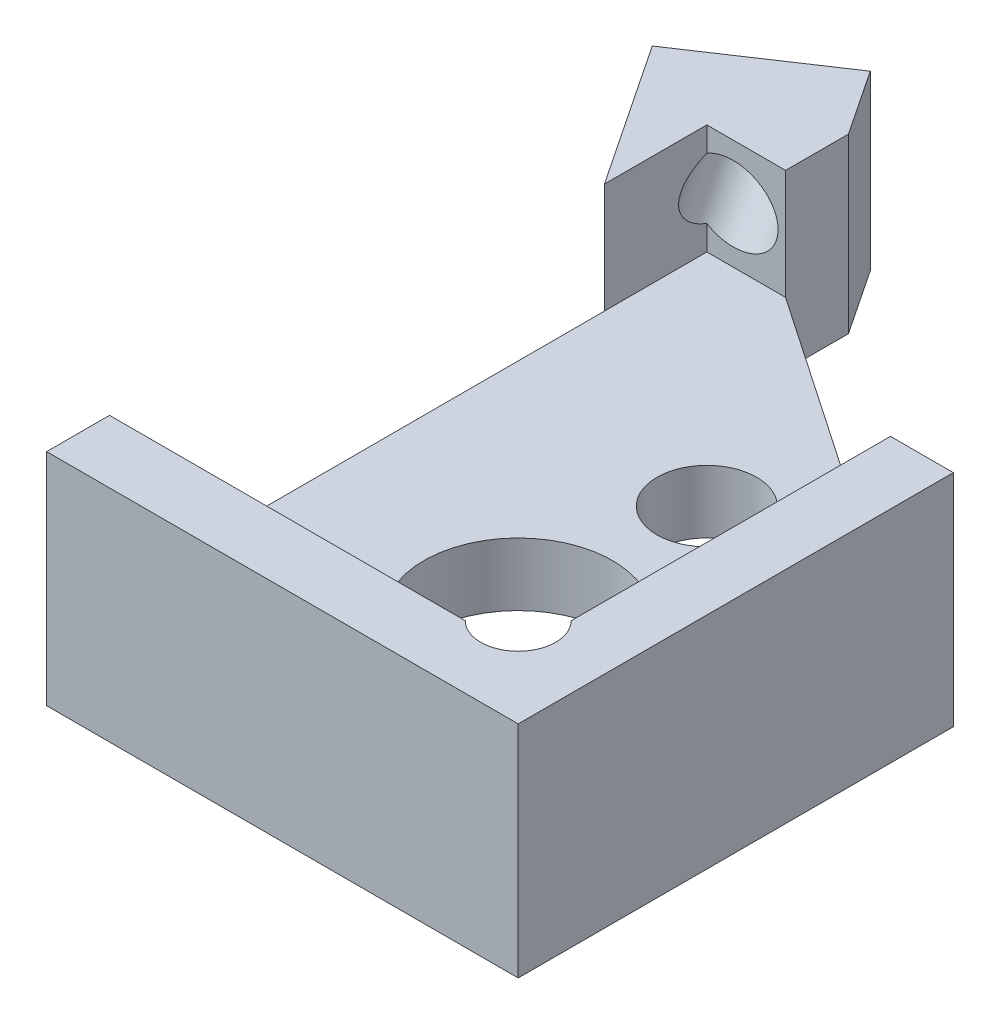
SolidWorks part; units mm, degrees
ref_plane "Front Plane" through (0, 0, 0) normal (0, 0, 1) x (1, 0, 0)
ref_plane "Top Plane" through (0, 0, 0) normal (0, 1, 0) x (1, 0, 0)
ref_plane "Right Plane" through (0, 0, 0) normal (1, 0, 0) x (0, 0, -1)
sketch "Sketch1" plane through (0, 0, 0) normal (0, 1, 0) x (1, 0, 0)
  line L7 (4.25, 5.75) -> (-4.25, 5.75)
  line L8 (4.25, 5.75) -> (4.25, -5.75)
  line L9 (4.25, -5.75) -> (-4.25, -5.75)
  line L10 (-4.25, 5.75) -> (-4.25, -5.75)
  line L11 (4.25, 5.75) -> (-4.25, -5.75) construction
  line L12 (4.25, -5.75) -> (-4.25, 5.75) construction
  point P0 (0, 0)
  point P6 (0, 0)
  dimension "D1" = 8.5
  dimension "D2" = 11.5
extrude "Boss-Extrude1" add sketch "Sketch1" along normal blind 3.5
sketch "Sketch2" plane through (0, 3.5, 0) normal (0, 1, 0) x (1, 0, 0)
  line L0 (-4.25, 5.75) -> (-4.25, -5.75) construction
  line L1 (3.25, 4.75) -> (-3.25, 4.75)
  line L2 (3.25, 4.75) -> (3.25, -4.75)
  line L3 (3.25, -4.75) -> (-3.25, -4.75)
  line L4 (-3.25, 4.75) -> (-3.25, -4.75)
  line L5 (3.25, 4.75) -> (-3.25, -4.75) construction
  line L6 (3.25, -4.75) -> (-3.25, 4.75) construction
  line L7 (4.25, 5.75) -> (-4.25, 5.75) construction
  point P0 (0, 0)
  dimension "D1" = 1
  dimension "D2" = 1
extrude "Cut-Extrude1" cut sketch "Sketch2" against normal offset from surface (2.5 mm away) 1 up to face at (0, 0, 0)
sketch "Sketch3" plane through (0, 1, 0) normal (0, 1, 0) x (1, 0, 0)
  line L0 (-3.25, -4.75) -> (3.25, -4.75) construction
  line L1 (3.25, -4.75) -> (3.25, 4.75) construction
  circle A0 centre (0.25, -1.75) radius 1.5
  dimension "D1" = 3
  dimension "D2" = 3
  dimension "D3" = 3
extrude "Cut-Extrude2" cut sketch "Sketch3" against normal through all
sketch "Sketch6" plane through (0, 3.5, 0) normal (0, 1, 0) x (1, 0, 0)
  line L0 (3.25, -4.75) -> (3.25, 4.75) construction
  line L2 (-3.25, -4.75) -> (3.25, -4.75) construction
  line L3 (3.25, -4.3291) -> (2.8291, -4.3291) construction
  line L4 (2.8291, -4.3291) -> (2.8291, -4.75) construction
  circle A3 centre (2.8291, -4.3291) radius 0.5953
  dimension "D1" = 1.1906
extrude "Cut-Extrude5" cut sketch "Sketch6" against normal up to surface (2.5 mm away) up to face at (0.25, 1, 3.25)
sketch "Sketch7" plane through (0, 1, 0) normal (0, 1, 0) x (1, 0, 0)
  line L0 (2.125, 1.25) -> (-1.625, 1.25) construction
  line L1 (-1.625, 1.25) -> (-1.625, -3.5) construction
  line L2 (-1.625, -3.5) -> (2.125, -3.5) construction
  line L3 (2.125, -3.5) -> (2.125, 1.25) construction
  line L4 (0.25, 1.25) -> (0.25, -1.75) construction
  circle A0 centre (0.25, 1.25) radius 0.7937
  circle A2 centre (-1.625, -3.5) radius 0.7938
  circle A3 centre (2.125, -3.5) radius 0.7938
  circle A4 centre (0.25, -1.75) radius 1.5 construction
  dimension "D1" = 1.5875
  dimension "D2" = 3.75
  dimension "D3" = 3
  dimension "D4" = 1.75
extrude "Cut-Extrude6" cut sketch "Sketch7" against normal through all
sketch "Sketch9" plane through (0, 3.5, 0) normal (0, 1, 0) x (1, 0, 0)
  line L0 (-2.6906, 6.7896) -> (-4.7708, 5.4028)
  line L1 (-3.4116, 4.6422) -> (-4.0015, 4.249)
  line L2 (-3.4116, 4.6422) -> (-2.5113, 5.2425)
  line L3 (-2.6906, 6.7896) -> (-1.9214, 5.6357)
  line L4 (3.25, -4.75) -> (-2.75, 4.25) construction
  line L5 (3.25, -4.75) -> (-2.75, -4.75) construction
  line L6 (-3.25, -4.75) -> (2.4081, -4.75) construction
  line L8 (-2.75, -4.75) -> (-2.75, 4.25) construction
  line L9 (-2.75, 4.25) -> (3.25, 4.25) construction
  line L10 (3.25, -3.9081) -> (3.25, 4.75) construction
  line L11 (3.25, 4.25) -> (3.25, -4.75) construction
  line L12 (-2.75, 3.6498) -> (-1.8497, 4.25) construction
  line L13 (-2.75, 3.6498) -> (-3.4116, 4.6422) construction
  line L14 (-2.2998, 3.9499) -> (-2.9615, 4.9423) construction
  line L15 (-1.9214, 5.6357) -> (-2.5113, 5.2425)
  line L16 (-4.0015, 4.249) -> (-4.7708, 5.4028)
  line L17 (-2.9615, 4.9423) -> (-3.7307, 6.0962) construction
  arc A0 (2.4081, -4.75) -> (3.25, -3.9081) centre (2.8291, -4.3291) ccw construction
  dimension "D1" = 6
  dimension "D2" = 9
  dimension "D3" = 1.082
  dimension "D4" = 2.5
extrude "Boss-Extrude2" add sketch "Sketch9" against normal up to surface (3.5 mm away) up to face at (2.125, 0, 4.2938)
sketch "Sketch14" plane through (0, 3.5, 0) normal (0, 1, 0) x (1, 0, 0)
  line L1 (-6.2326, 2.1835) -> (-0.2674, 2.1835)
  line L2 (-6.2326, 2.1835) -> (-6.2326, 7.3165)
  line L3 (-6.2326, 7.3165) -> (-0.2674, 7.3165)
  line L4 (-0.2674, 2.1835) -> (-0.2674, 7.3165)
  line L5 (-6.2326, 2.1835) -> (-0.2674, 7.3165) construction
  line L6 (-6.2326, 7.3165) -> (-0.2674, 2.1835) construction
  point P0 (-3.25, 4.75)
extrude "Cut-Extrude8" cut sketch "Sketch14" against normal blind 0.75
sketch "Sketch10" plane through (-3.9615, 0, -5.9423) normal (-0.5547, 0, -0.8321) x (-0.8321, 0, 0.5547)
  line L0 (-0.2774, 1) -> (-0.2774, 1.875) construction
  line L1 (-1.5274, 2.75) -> (0.9726, 2.75) construction
  line L2 (-0.2774, 1.875) -> (-0.2774, 2.75) construction
  line L4 (-0.2774, 1) -> (-0.2774, 0) construction
  line L5 (-1.5274, 0) -> (0.9726, 0) construction
  dimension "D1" = 1
hole_wizard "Tap Drill for #0-80 Tap1" positions "Sketch12" profile "Sketch11" hole size "#0-80" standard "ANSI Inch"
sketch "Sketch12" plane through (-3.9615, 0, -5.9423) normal (-0.5547, 0, -0.8321) x (-0.8321, 0, 0.5547)
  point P0 (-0.2774, 1.875)
sketch "Sketch11" plane through (-3.7307, 1.875, -6.0962) normal (0, 1, 0) x (-0.8321, 0, 0.5547)
  line L0 (0, 0) -> (0, 7.4679)
  line L1 (0, 7.4679) -> (0.5956, 7.11)
  line L2 (0.5956, 7.11) -> (0.5956, 0)
  line L5 (0.5956, 0) -> (0, 0)
  line L10 (0, 7.4679) -> (-0.5956, 7.11) construction
  line L11 (0, -6.35) -> (0, 107.95) construction
  dimension "Hole Dia." = 1.1913
  dimension "Hole Depth" = 7.11
  dimension "Drill Angle" = 118
sketch "Sketch13" plane through (0, 3.5, 0) normal (0, 1, 0) x (1, 0, 0)
  line L0 (-1.9976, 5.75) -> (-1.9976, 4.75)
  line L2 (-1.625, -3.5) -> (-3.25, -3.5) construction
  line L3 (3.25, 1.1708) -> (4.25, 1.1708)
  line L4 (4.25, -5.75) -> (4.25, 5.75) construction
  line L5 (4.25, 1.1708) -> (4.25, 5.75)
  line L6 (4.25, 5.75) -> (-1.9976, 5.75)
  line L7 (-4.25, 4.6217) -> (-3.25, 3.1217)
  line L8 (-3.25, 2.1835) -> (-3.25, -4.75) construction
  line L9 (-4.25, 2.1835) -> (-4.25, -5.75) construction
  line L10 (-3.25, 3.1217) -> (-3.25, -5.75)
  line L11 (-4.25, -5.75) -> (4.25, -5.75) construction
  line L12 (-3.25, -5.75) -> (-4.25, -5.75)
  line L13 (-4.25, -5.75) -> (-4.25, 4.6217)
  line L15 (-4.7708, 5.4028) -> (-4.25, 4.6217) construction
  line L17 (-1.9976, 4.75) -> (3.25, 1.1708)
  line L18 (3.25, -3.9081) -> (3.25, 4.75) construction
  line L20 (0.25, 1.25) -> (1.1656, 2.5925) construction
  line L23 (3.25, 4.75) -> (-0.2674, 4.75) construction
extrude "Cut-Extrude7" cut sketch "Sketch13" against normal up to next
